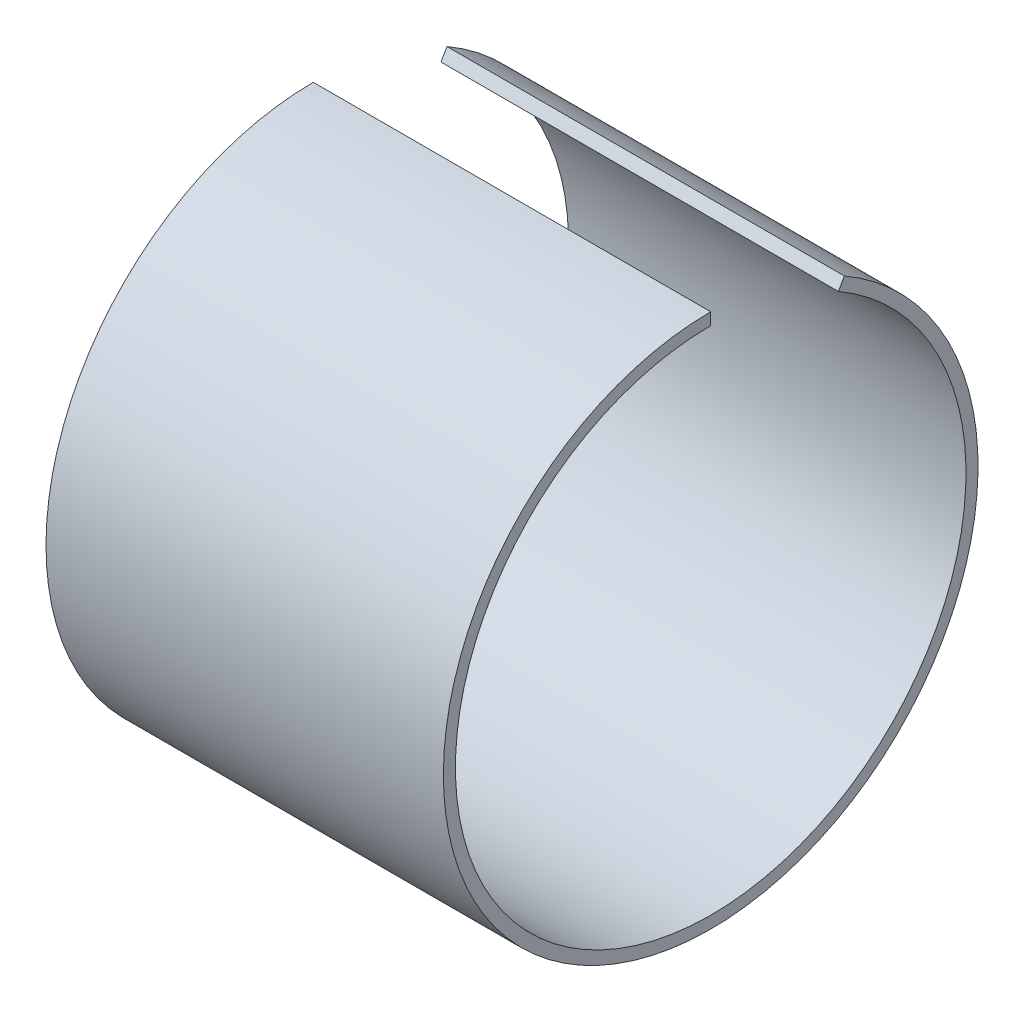
SolidWorks part; units mm, degrees
material "Chrome Stainless Steel"
ref_plane "Front" through (0, 0, 0) normal (0, 0, 1) x (1, 0, 0)
ref_plane "Top" through (0, 0, 0) normal (0, 1, 0) x (1, 0, 0)
ref_plane "Right" through (0, 0, 0) normal (1, 0, 0) x (0, 0, -1)
sketch "Sketch1" plane through (0, 0, 0) normal (0, 0, 1) x (1, 0, 0)
  line L0 (0, 0) -> (33, 0) construction
  line L1 (0, 21.2) -> (33, 21.2)
  line L2 (0, 21.2) -> (0, 22.2)
  line L3 (0, 22.2) -> (33, 22.2)
  line L4 (33, 22.2) -> (33, 21.2)
  dimension "D1" = 33
  dimension "D2" = 21.2
  dimension "D3" = 1
  dimension "D4" = 33
revolve "Revolve1" add sketch "Sketch1" angle 330 about L0
